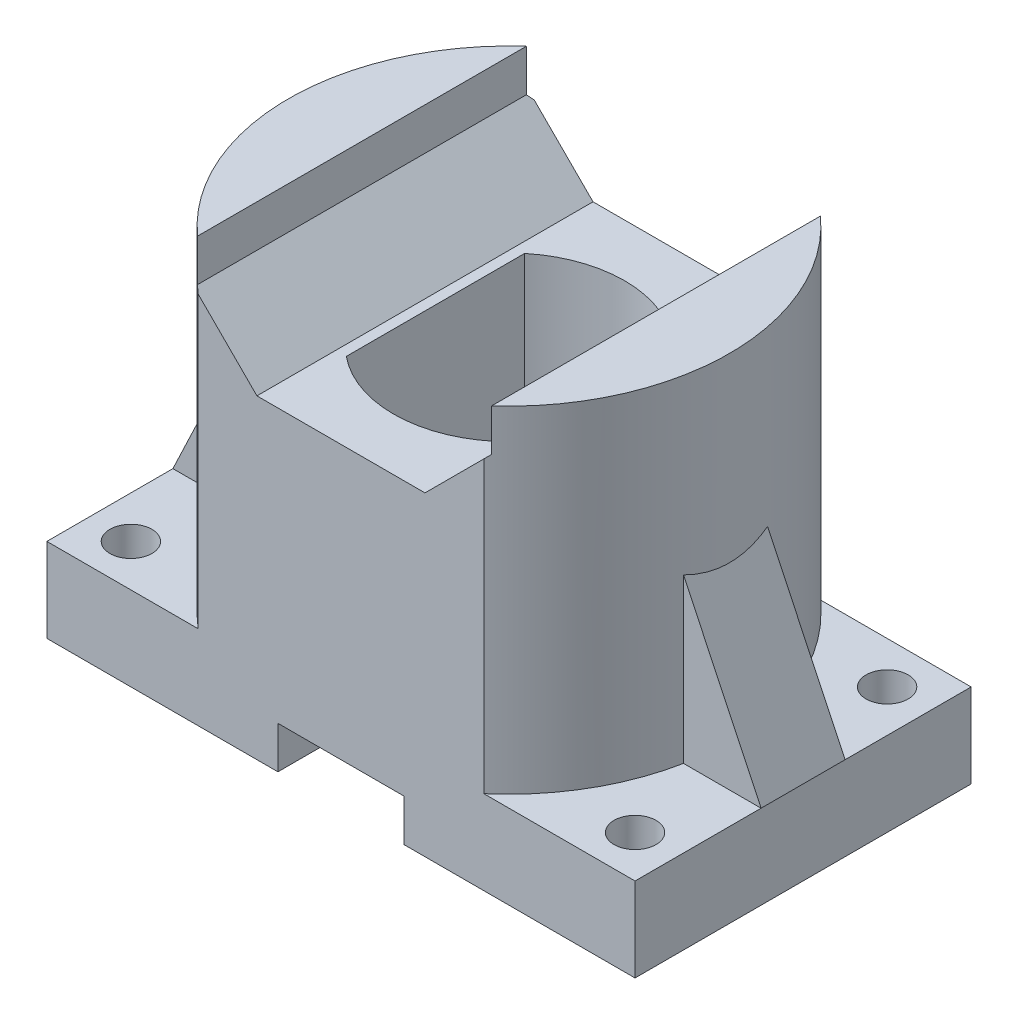
SolidWorks part; units mm, degrees
ref_plane "Спереди" through (0, 0, 0) normal (0, 0, 1) x (1, 0, 0)
ref_plane "Сверху" through (0, 0, 0) normal (0, 1, 0) x (1, 0, 0)
ref_plane "Справа" through (0, 0, 0) normal (1, 0, 0) x (0, 0, -1)
sketch "Эскиз1" plane through (0, 0, 0) normal (0, 1, 0) x (1, 0, 0)
  line L0 (0, 0) -> (-70, 0) construction
  line L1 (-70, 40) -> (70, 40)
  line L2 (-70, 40) -> (-70, -40)
  line L3 (-70, -40) -> (70, -40)
  line L4 (70, 40) -> (70, -40)
  line L5 (-70, 40) -> (70, -40) construction
  line L6 (-70, -40) -> (70, 40) construction
  line L7 (0, 0) -> (0, 40) construction
  circle A0 centre (-60, 30) radius 5
  circle A1 centre (60, 30) radius 5
  circle A2 centre (60, -30) radius 5
  circle A3 centre (-60, -30) radius 5
  point P0 (0, 0)
  dimension "D3" = 10
  dimension "D1" = 140
  dimension "D2" = 80
  dimension "D4" = 30
  dimension "D5" = 10
extrude "Бобышка-Вытянуть1" add sketch "Эскиз1" along normal blind 20
sketch "Эскиз2" plane through (0, 20, 0) normal (0, 1, 0) x (1, 0, 0)
  line L0 (-34.0037, 40) -> (34.0037, 40)
  line L1 (70, 40) -> (-70, 40) construction
  line L2 (-34.0037, -40) -> (34.0037, -40)
  line L3 (-70, -40) -> (70, -40) construction
  arc A0 (-34.0037, 40) -> (-34.0037, -40) centre (0, 0) ccw
  arc A1 (34.0037, -40) -> (34.0037, 40) centre (0, 0) ccw
  dimension "D1" = 105
extrude "Бобышка-Вытянуть2" add sketch "Эскиз2" along normal blind 80
sketch "Эскиз3" plane through (0, 100, 0) normal (0, 1, 0) x (1, 0, 0)
  line L0 (17.5, -21.2132) -> (17.5, 21.2132)
  line L3 (-17.5, -21.2132) -> (-17.5, 21.2132)
  line L4 (0, -44) -> (0, 44) construction
  arc A0 (17.5, 21.2132) -> (-17.5, 21.2132) centre (0, 0) ccw
  arc A1 (-17.5, -21.2132) -> (17.5, -21.2132) centre (0, 0) ccw
  dimension "D1" = 55
  dimension "D2" = 17.5
  dimension "D3" = 17.5
extrude "Вырез-Вытянуть1" cut sketch "Эскиз3" against normal blind 65
sketch "Эскиз5" plane through (0, 0, 0) normal (0, 0, 1) x (1, 0, 0)
  line L0 (-20, 75) -> (20, 75)
  line L1 (0, 75) -> (0, 25.9095) construction
  line L2 (0, -44) -> (0, 44) construction
  line L3 (20, 75) -> (35, 90)
  line L4 (35, 100) -> (35, 90)
  line L5 (52.5, 100) -> (34.0037, 100) construction
  line L6 (34.0037, 100) -> (-34.0037, 100) construction
  line L7 (-20, 75) -> (-35, 90)
  line L8 (-35, 100) -> (-35, 90)
  line L9 (35, 100) -> (-35, 100)
  point P17 (0, 75)
  dimension "D1" = 35
  dimension "D2" = 20
  dimension "D3" = 10
  dimension "D5" = 25
extrude "Вырез-Вытянуть2" cut sketch "Эскиз5" against normal through all both and the other way through all
sketch "Эскиз6" plane through (0, 0, 0) normal (0, 0, 1) x (1, 0, 0)
  line L0 (15, 10) -> (15, 0)
  line L1 (44, 0) -> (-44, 0) construction
  line L2 (15, 0) -> (-15, 0)
  line L5 (-15, 10) -> (15, 10)
  line L6 (-15, 10) -> (-15, 0)
  point P5 (0, 0)
  point P6 (-15, 0)
  point P7 (-15, 10)
  dimension "D1" = 15
  dimension "D2" = 10
  dimension "D3" = 15
extrude "Вырез-Вытянуть3" cut sketch "Эскиз6" against normal through all both and the other way through all
sketch "Эскиз7" plane through (0, 0, 0) normal (0, -1, 0) x (1, 0, 0)
  circle A0 centre (0, 0) radius 25
  dimension "D1" = 50
extrude "Вырез-Вытянуть4" cut sketch "Эскиз7" against normal blind 35
sketch "Эскиз8" plane through (0, 0, 0) normal (0, 0, 1) x (1, 0, 0)
  line L0 (-70, 20) -> (-51, 60)
  line L1 (-51, 60) -> (-51, 20)
  line L2 (-70, 20) -> (-34.0037, 20) construction
  line L3 (-51, 20) -> (-70, 20)
  line L4 (0, -44) -> (0, 44) construction
  line L5 (51, 60) -> (51, 20)
  line L6 (51, 20) -> (70, 20)
  line L7 (70, 20) -> (51, 60)
  point P3 (-51.3454, 60)
  dimension "D1" = 40
  dimension "D2" = 19
extrude "Бобышка-Вытянуть3" add sketch "Эскиз8" along normal blind 10 and the other way blind 10
